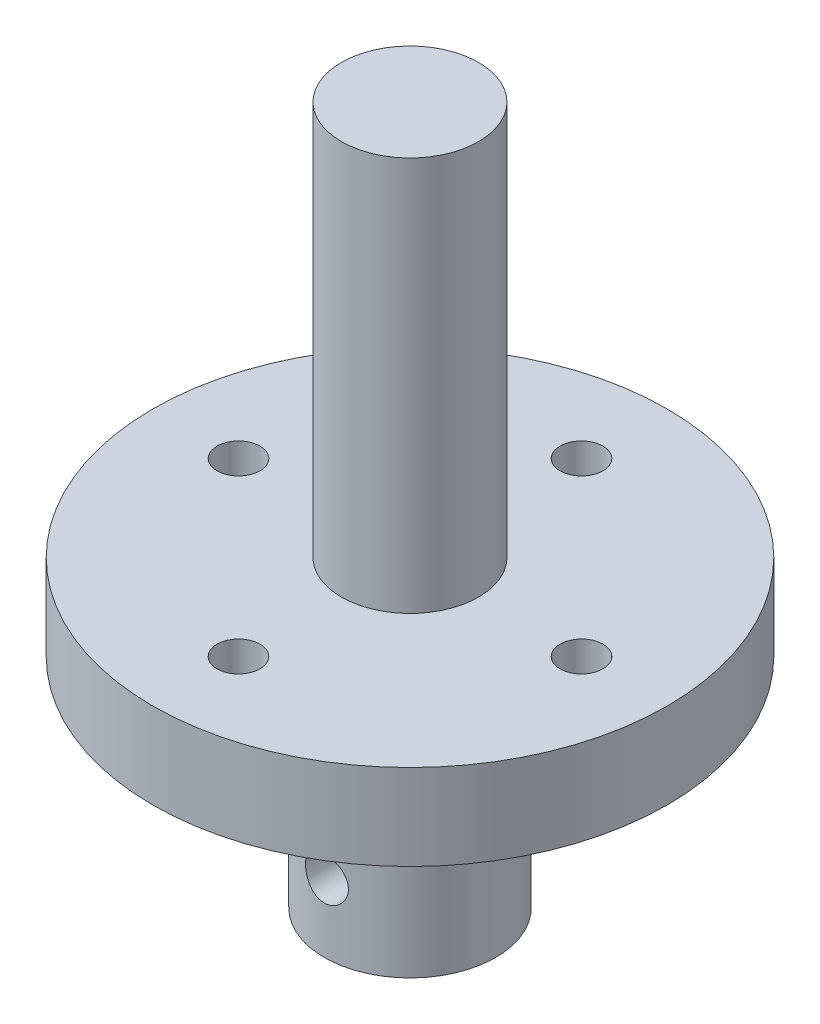
SolidWorks part; units mm, degrees
ref_plane "Front Plane" through (0, 0, 0) normal (0, 0, 1) x (1, 0, 0)
ref_plane "Top Plane" through (0, 0, 0) normal (0, 1, 0) x (1, 0, 0)
ref_plane "Right Plane" through (0, 0, 0) normal (1, 0, 0) x (0, 0, -1)
sketch "Sketch1" plane through (0, 0, 0) normal (0, 1, 0) x (1, 0, 0)
  circle A0 centre (0, 0) radius 15
  dimension "D1" = 30
extrude "Boss-Extrude1" add sketch "Sketch1" along normal blind 5
sketch "Sketch2" plane through (0, 0, 0) normal (0, -1, 0) x (1, 0, 0)
  circle A0 centre (0, 0) radius 5
  dimension "D1" = 10
extrude "Boss-Extrude2" add sketch "Sketch2" along normal blind 12.7
sketch "Sketch3" plane through (0, -12.7, 0) normal (0, -1, 0) x (1, 0, 0)
  circle A0 centre (0, 0) radius 2
  dimension "D1" = 4
extrude "Cut-Extrude1" cut sketch "Sketch3" against normal blind 9.5
sketch "Sketch5" plane through (0, 5, 0) normal (0, 1, 0) x (1, 0, 0)
  line L0 (0, -25) -> (0, 25) construction
  circle A3 centre (0, -10) radius 1.25
  circle A4 centre (0, 0) radius 5 construction
  dimension "D3" = 2.5
  dimension "D4" = 10
extrude "Cut-Extrude2" cut sketch "Sketch5" against normal blind 5
pattern_circular "CirPattern1" count 4 over 360 about axis through (0, 0, 0) along (0, 1, 0) of "Cut-Extrude2"
sketch "Sketch8" plane through (0, 5, 0) normal (0, 1, 0) x (1, 0, 0)
  point P0 (-10, 0)
  point P3 (0, -10)
  point P6 (10, 0)
  point P9 (0, 10)
hole_wizard "M3x0.5 Tapped Hole1" positions "Sketch8" profile "Sketch7" tap size "M3x0.5" standard "ANSI Metric" end condition through all
sketch "Sketch7" plane through (-10, 5, 0) normal (1, 0, 0) x (0, 0, 1)
  line L0 (0, 0) -> (0, 17.7)
  line L1 (0, 17.7) -> (1.25, 17.7)
  line L2 (1.25, 17.7) -> (1.25, 0)
  line L5 (1.25, 0) -> (0, 0)
  line L11 (0, -6.35) -> (0, 107.95) construction
  dimension "Thru Tap Drill Dia." = 2.5
  dimension "Thru Tap Drill Depth" = 17.7
ref_plane "Plane1" through (0, 0, 5) normal (0, 0, 1) x (1, 0, 0)
sketch "Sketch9" plane through (0, 0, 5) normal (0, 0, 1) x (1, 0, 0)
  line L0 (-5, -12.7) -> (5, -12.7) construction
  line L3 (0, 0) -> (0, -5.0183) construction
  circle A0 centre (0, -8.7) radius 1.25
  point P0 (0, -8.7)
  dimension "D1" = 2.5
  dimension "D2" = 4
hole_wizard "M3x0.5 Tapped Hole2" positions "Sketch9" profile "Sketch11" tap size "M3x0.5" standard "ANSI Metric"
sketch "Sketch11" plane through (0, -8.7, 5) normal (1, 0, 0) x (0, -1, 0)
  line L0 (0, 0) -> (0, 5.7501)
  line L1 (0, 5.7501) -> (1.25, 4.999)
  line L2 (1.25, 4.999) -> (1.25, 0)
  line L5 (1.25, 0) -> (0, 0)
  line L10 (0, 5.7501) -> (-1.25, 4.999) construction
  line L11 (0, -6.35) -> (0, 107.95) construction
  dimension "Tap Drill Dia." = 2.5
  dimension "Tap Drill Depth" = 4.999
  dimension "Drill Angle" = 118
cosmetic thread "Hole Thread5" parameters "D1"=3, "D2"=3
sketch "Sketch12" plane through (0, 5, 0) normal (0, 1, 0) x (1, 0, 0)
  circle A0 centre (0, 0) radius 4
  dimension "D1" = 8
extrude "Boss-Extrude3" add sketch "Sketch12" along normal blind 23 contours A0
